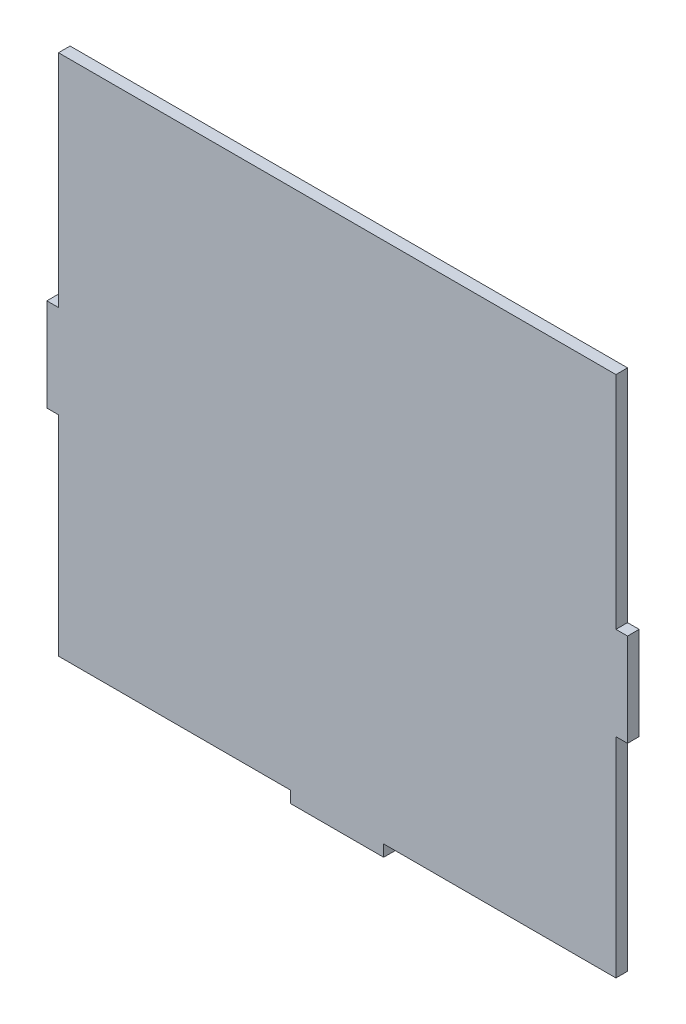
SolidWorks part; units mm, degrees
ref_plane "Plan de face" through (0, 0, 0) normal (0, 0, 1) x (1, 0, 0)
ref_plane "Plan de dessus" through (0, 0, 0) normal (0, 1, 0) x (1, 0, 0)
ref_plane "Plan de droite" through (0, 0, 0) normal (1, 0, 0) x (0, 0, -1)
sketch "Esquisse1" plane through (0, 0, 0) normal (0, 0, 1) x (1, 0, 0)
  line L13 (0, -206.5198) -> (348.1503, -206.5198) construction
  line L21 (5, -91.5198) -> (245, -91.5198)
  line L22 (0, -186.5198) -> (0, -226.5198)
  line L23 (105, -321.5198) -> (145, -321.5198)
  line L25 (125, 0) -> (125, -362.0025) construction
  line L26 (5, -91.5198) -> (5, -186.5198)
  line L27 (5, -186.5198) -> (0, -186.5198)
  line L28 (0, -226.5198) -> (5, -226.5198)
  line L29 (5, -226.5198) -> (5, -316.5198)
  line L30 (5, -316.5198) -> (105, -316.5198)
  line L31 (105, -316.5198) -> (105, -321.5198)
  line L32 (145, -316.5198) -> (145, -321.5198)
  line L33 (145, -316.5198) -> (245, -316.5198)
  line L38 (245, -91.5198) -> (245, -186.5198)
  line L39 (245, -186.5198) -> (250, -186.5198)
  line L40 (250, -186.5198) -> (250, -226.5198)
  line L41 (250, -226.5198) -> (245, -226.5198)
  line L42 (245, -226.5198) -> (245, -316.5198)
  dimension "D1" = 5
  dimension "D2" = 20
  dimension "D3" = 125
  dimension "D4" = 115
  dimension "D5" = 5
  dimension "D6" = 20
  dimension "D7" = 20
  dimension "D8" = 20
  dimension "D9" = 125
  dimension "D10" = 115
  dimension "D11" = 5
  dimension "D12" = 40
extrude "Boss.-Extru.1" add sketch "Esquisse1" along normal blind 5
